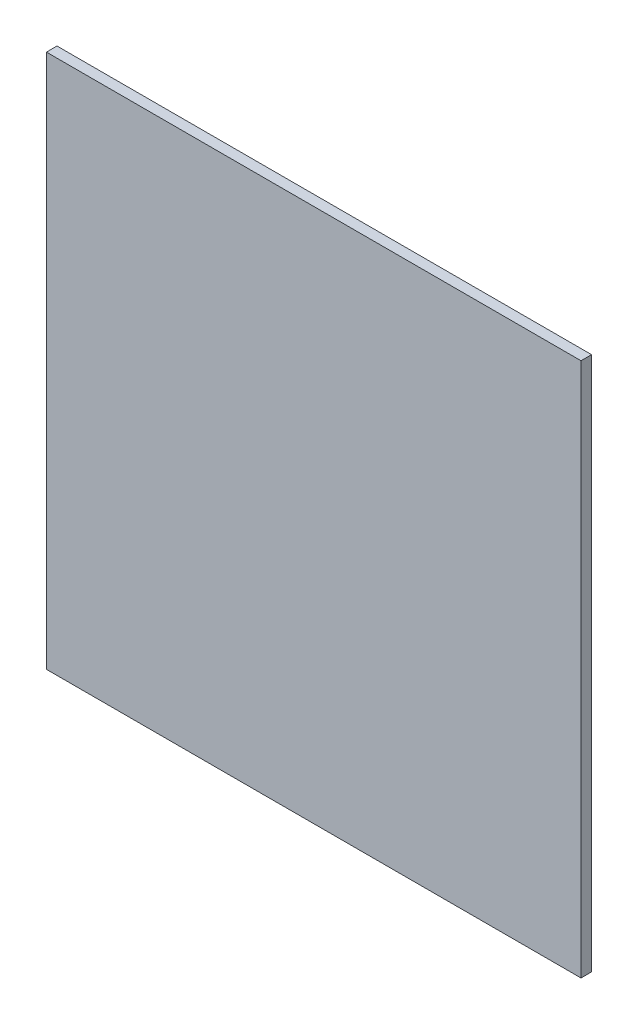
SolidWorks part; units mm, degrees
material "Glass"
ref_plane "Front Plane" through (0, 0, 0) normal (0, 0, 1) x (1, 0, 0)
ref_plane "Top Plane" through (0, 0, 0) normal (0, 1, 0) x (1, 0, 0)
ref_plane "Right Plane" through (0, 0, 0) normal (1, 0, 0) x (0, 0, -1)
sketch "Sketch1" plane through (0, 0, 0) normal (0, 0, 1) x (1, 0, 0)
  line L1 (-120.65, -120.65) -> (120.65, -120.65)
  line L2 (-120.65, -120.65) -> (-120.65, 120.65)
  line L3 (-120.65, 120.65) -> (120.65, 120.65)
  line L4 (120.65, -120.65) -> (120.65, 120.65)
  line L5 (-120.65, -120.65) -> (120.65, 120.65) construction
  line L6 (-120.65, 120.65) -> (120.65, -120.65) construction
  point P0 (0, 0)
  dimension "D1" = 241.3
  dimension "D2" = 241.3
extrude "Boss-Extrude1" add sketch "Sketch1" along normal blind 4.7625
